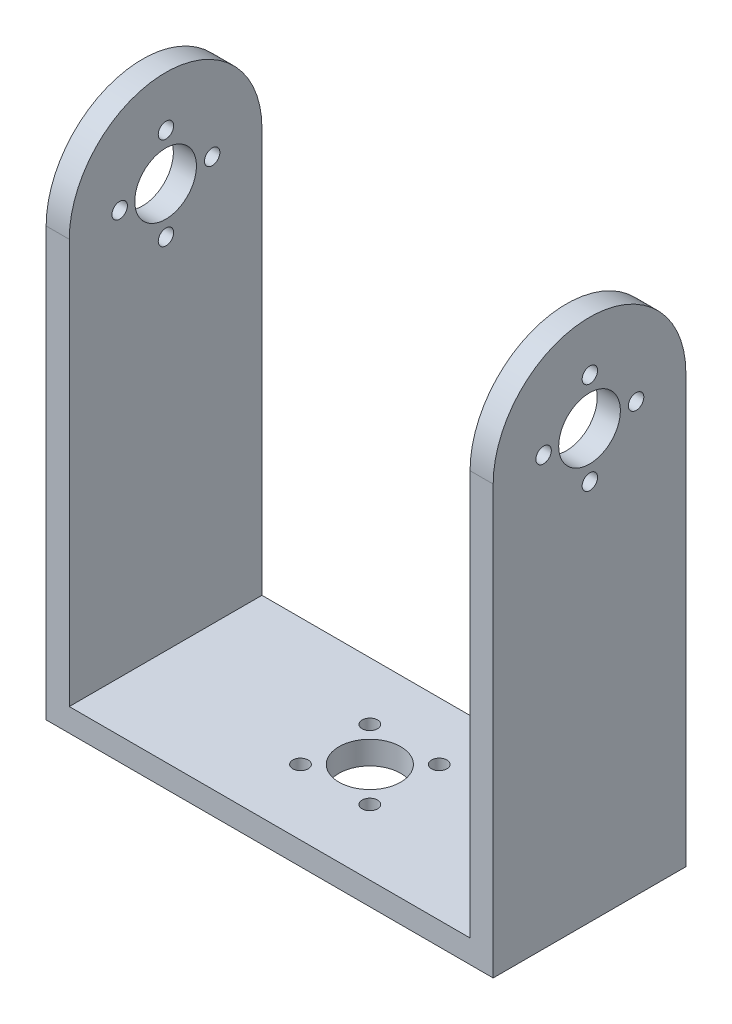
SolidWorks part; units mm, degrees
ref_plane "Front Plane" through (0, 0, 0) normal (0, 0, 1) x (1, 0, 0)
ref_plane "Top Plane" through (0, 0, 0) normal (0, 1, 0) x (1, 0, 0)
ref_plane "Right Plane" through (0, 0, 0) normal (1, 0, 0) x (0, 0, -1)
sketch "Sketch1" plane through (0, 0, 0) normal (0, 1, 0) x (1, 0, 0)
  line L1 (0, 0) -> (58, 0)
  line L2 (0, 0) -> (0, 25)
  line L3 (0, 25) -> (58, 25)
  line L4 (58, 0) -> (58, 25)
  dimension "D1" = 58
  dimension "D2" = 25
extrude "Boss-Extrude1" add sketch "Sketch1" along normal blind 3
sketch "Sketch2" plane through (0, 3, 0) normal (0, 1, 0) x (1, 0, 0)
  line L0 (0, 0) -> (58, 0) construction
  line L1 (58, 25) -> (55, 25)
  line L2 (58, 25) -> (58, 0)
  line L3 (58, 0) -> (55, 0)
  line L4 (55, 25) -> (55, 0)
  line L6 (0, 25) -> (3, 25)
  line L7 (0, 25) -> (0, 0)
  line L8 (0, 0) -> (3, 0)
  line L9 (3, 25) -> (3, 0)
  dimension "D1" = 3
  dimension "D2" = 3
extrude "Boss-Extrude2" add sketch "Sketch2" along normal blind 65
sketch "Sketch3" plane through (0, 0, 0) normal (-1, 0, 0) x (0, 0, 1)
  line L0 (-25, 68) -> (-25, 0) construction
  line L1 (0, 68) -> (0, 0) construction
  line L2 (-25, 68) -> (0, 68) construction
  line L3 (-25, 55.5) -> (-25, 68)
  line L5 (-25, 55.5) -> (-25, 68)
  line L6 (-25, 68) -> (0, 68)
  line L7 (0, 55.5) -> (0, 68)
  line L8 (-12.5, 68) -> (0, 68)
  arc A0 (-25, 55.5) -> (0, 55.5) centre (-12.5, 55.5) cw
  point P9 (-12.5, 68)
  point P10 (-12.5, 68)
  line M2 (0, 0) -> (0, 68)
  line M3 (0, 68) -> (-25, 68)
  line M4 (-25, 68) -> (-25, 0)
  dimension "D1" = 12.5
extrude "Cut-Extrude1" cut sketch "Sketch3" against normal blind 65 contours A0 L6 M4 | A0 M3 M2
sketch "Sketch4" plane through (0, 0, 0) normal (-1, 0, 0) x (0, 0, 1)
  line L0 (-25, 55.5) -> (-12.5, 55.5) construction
  line L1 (-12.5, 68) -> (-12.5, 33.517) construction
  circle A0 centre (-12.5, 55.5) radius 4
  arc A1 (0, 55.5) -> (-25, 55.5) centre (-12.5, 55.5) ccw construction
  dimension "D1" = 8
extrude "Cut-Extrude2" cut sketch "Sketch4" against normal blind 65
sketch "Sketch5" plane through (3, 0, 0) normal (1, 0, 0) x (0, 0, -1)
  circle A0 centre (12.5437, 61.5) radius 1
  circle A1 centre (18.5437, 55.5) radius 1
  circle A2 centre (6.5437, 55.5) radius 1
  circle A3 centre (12.5437, 49.5) radius 1
  dimension "D1" = 2
  dimension "D2" = 2
  dimension "D3" = 2
  dimension "D4" = 2
extrude "Cut-Extrude3" cut sketch "Sketch5" against normal through all both and the other way through all
sketch "Sketch7" plane through (0, 0, 0) normal (0, -1, 0) x (-1, 0, 0)
  circle A0 centre (-29, 13) radius 4
  circle A1 centre (-24.5, 17.5) radius 1
  circle A2 centre (-33.5, 17.5) radius 1
  circle A3 centre (-33.5, 8.5) radius 1
  circle A4 centre (-24.5, 8.5) radius 1
  dimension "D1" = 8
  dimension "D2" = 2
  dimension "D3" = 2
  dimension "D4" = 2
  dimension "D5" = 2
extrude "Cut-Extrude5" cut sketch "Sketch7" against normal up to next
